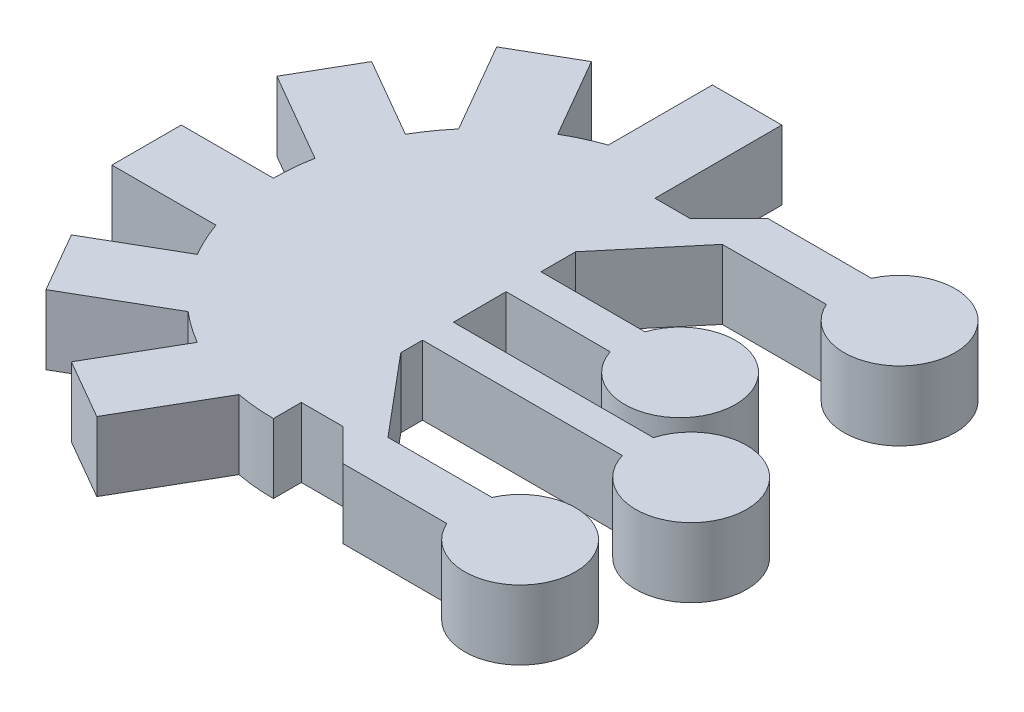
SolidWorks part; units mm, degrees
material "Pure Gold"
ref_plane "Front Plane" through (0, 0, 0) normal (0, 0, 1) x (1, 0, 0)
ref_plane "Top Plane" through (0, 0, 0) normal (0, 1, 0) x (1, 0, 0)
ref_plane "Right Plane" through (0, 0, 0) normal (1, 0, 0) x (0, 0, -1)
sketch "Sketch1" plane through (0, 0, 0) normal (0, 1, 0) x (1, 0, 0)
  line L0 (0, 75.2345) -> (0, 20) construction
  line L1 (-87.4253, 0) -> (88.6443, 0) construction
  line L2 (-10, 43.2843) -> (-10, 28.2843)
  line L3 (-10, 43.2843) -> (0, 43.2843)
  line L4 (0, 43.2843) -> (0, 30)
  line L23 (-12.9819, -42.4853) -> (-5.4819, -29.4949)
  line L24 (-12.9819, -42.4853) -> (-21.6421, -37.4853)
  line L25 (-21.6421, -37.4853) -> (-15, -25.9808)
  line L26 (-32.4853, -30.3024) -> (-19.4949, -22.8024)
  line L27 (-32.4853, -30.3024) -> (-37.4853, -21.6421)
  line L28 (-37.4853, -21.6421) -> (-25.9808, -15)
  line L29 (-43.2843, -10) -> (-28.2843, -10)
  line L30 (-43.2843, -10) -> (-43.2843, 0)
  line L31 (-43.2843, 0) -> (-30, 0)
  line L32 (-42.4853, 12.9819) -> (-29.4949, 5.4819)
  line L33 (-42.4853, 12.9819) -> (-37.4853, 21.6421)
  line L34 (-37.4853, 21.6421) -> (-25.9808, 15)
  line L35 (-30.3024, 32.4853) -> (-22.8024, 19.4949)
  line L36 (-30.3024, 32.4853) -> (-21.6421, 37.4853)
  line L37 (-21.6421, 37.4853) -> (-15, 25.9808)
  line L38 (0, 0) -> (0, 30) construction
  line L75 (0, 25) -> (5, 25)
  line L76 (12.9819, 42.4853) -> (5.4819, 29.4949)
  line L77 (12.9819, 42.4853) -> (21.6421, 37.4853)
  line L81 (21.6421, 37.4853) -> (15, 25.9808)
  line L82 (32.4853, 30.3024) -> (19.4949, 22.8024)
  line L83 (32.4853, 30.3024) -> (37.4853, 21.6421)
  line L87 (37.4853, 21.6421) -> (25.9808, 15)
  line L88 (43.2843, 10) -> (28.2843, 10)
  line L89 (43.2843, 10) -> (43.2843, 0)
  line L93 (43.2843, 0) -> (30, 0)
  line L94 (42.4853, -12.9819) -> (29.4949, -5.4819)
  line L96 (42.4853, -12.9819) -> (37.4853, -21.6421)
  line L99 (37.4853, -21.6421) -> (25.9808, -15)
  line L100 (30.3024, -32.4853) -> (22.8024, -19.4949)
  line L104 (30.3024, -32.4853) -> (21.6421, -37.4853)
  line L105 (21.6421, -37.4853) -> (15, -25.9808)
  line L106 (10, -43.2843) -> (10, -28.2843)
  line L109 (10, -43.2843) -> (0, -43.2843)
  line L111 (5, 25) -> (10.6066, 30.6066)
  line L113 (0, -25.9808) -> (0, -30)
  line L116 (10.6066, 30.6066) -> (25.6066, 30.6066)
  line L117 (0, 30) -> (0, 25)
  line L118 (0.9648, 12.6065) -> (10.6066, 24.0972)
  line L119 (0, -43.2843) -> (0, -30)
  line L120 (10.6066, 24.0972) -> (25.6066, 24.0972)
  line L121 (0, 12.9819) -> (0, -76.1053) construction
  line L122 (0.9648, 12.6065) -> (0.9648, 7.6065)
  line L123 (0.9648, 7.6065) -> (15.9648, 7.6065)
  line L124 (0.9404, 2.6065) -> (15.9404, 2.6065)
  line L125 (10.6066, -30.6066) -> (25.6066, -30.6066)
  line L126 (5.9808, -25.9808) -> (10.6066, -30.6066)
  line L127 (0.9648, -12.6065) -> (10.6066, -24.0972)
  line L128 (10.6066, -24.0972) -> (25.6066, -24.0972)
  line L129 (0.9404, 2.6065) -> (0.9526, -5)
  line L130 (0.9526, -5) -> (29.7774, -5)
  line L131 (0.9598, -9.469) -> (29.7774, -9.469)
  line L132 (0.9598, -9.469) -> (0.9648, -12.6065)
  line L133 (0, -25.9808) -> (5.9808, -25.9808)
  arc A0 (-10, 28.2843) -> (-15, 25.9808) centre (0, 0) ccw
  arc A1 (-22.8024, 19.4949) -> (-25.9808, 15) centre (0, 0) ccw
  arc A2 (-29.4949, 5.4819) -> (-30, 0) centre (0, 0) ccw
  arc A3 (-28.2843, -10) -> (-25.9808, -15) centre (0, 0) ccw
  arc A4 (-19.4949, -22.8024) -> (-15, -25.9808) centre (0, 0) ccw
  arc A5 (-5.4819, -29.4949) -> (0, -30) centre (0, 0) ccw
  arc A19 (19.8745, -2.2369) -> (20, 0) centre (0, 0) ccw
  arc A25 (25.6066, 30.6066) -> (25.6066, 24.0972) centre (32.9146, 27.3519) cw
  arc A26 (15.9648, 7.6065) -> (15.9404, 2.6065) centre (23.5518, 5.0694) cw
  arc A27 (25.6066, -30.6066) -> (25.6066, -24.0972) centre (32.9146, -27.3519) ccw
  arc A28 (29.7774, -5) -> (29.7774, -9.469) centre (37.459, -7.2345) cw
  arc A29 (0, 25) -> (0, -25.9808) centre (0, -0.4904) ccw
  dimension "D1" = 60
  dimension "D10" = 45
  dimension "D20" = 8
  dimension "D21" = 8
  dimension "D23" = 8
  dimension "D2" = 15
  dimension "D3" = 10
  dimension "D11" = 5
  dimension "D12" = 15
  dimension "D13" = 15
  dimension "D14" = 15
  dimension "D15" = 15
  dimension "D16" = 5
  dimension "D17" = 15
  dimension "D18" = 5
  dimension "D19" = 15
  dimension "D22" = 7.6065
  dimension "D4" = 12
extrude "Boss-Extrude1" add sketch "Sketch1" along normal blind 10 contours L113 A5 L23 L24 L25 A4 L26 L27 L28 A3 L29 L30 L31 A2 L32 L33 L34 A1 L35 L36 L37 A0 L2 L3 L4 L117 L75 L111 L116 A25 L120 L118 L122 L123 A26 L124 L129 L130 A28 L131 L132 L127 L128 A27 L125 L126 L133
